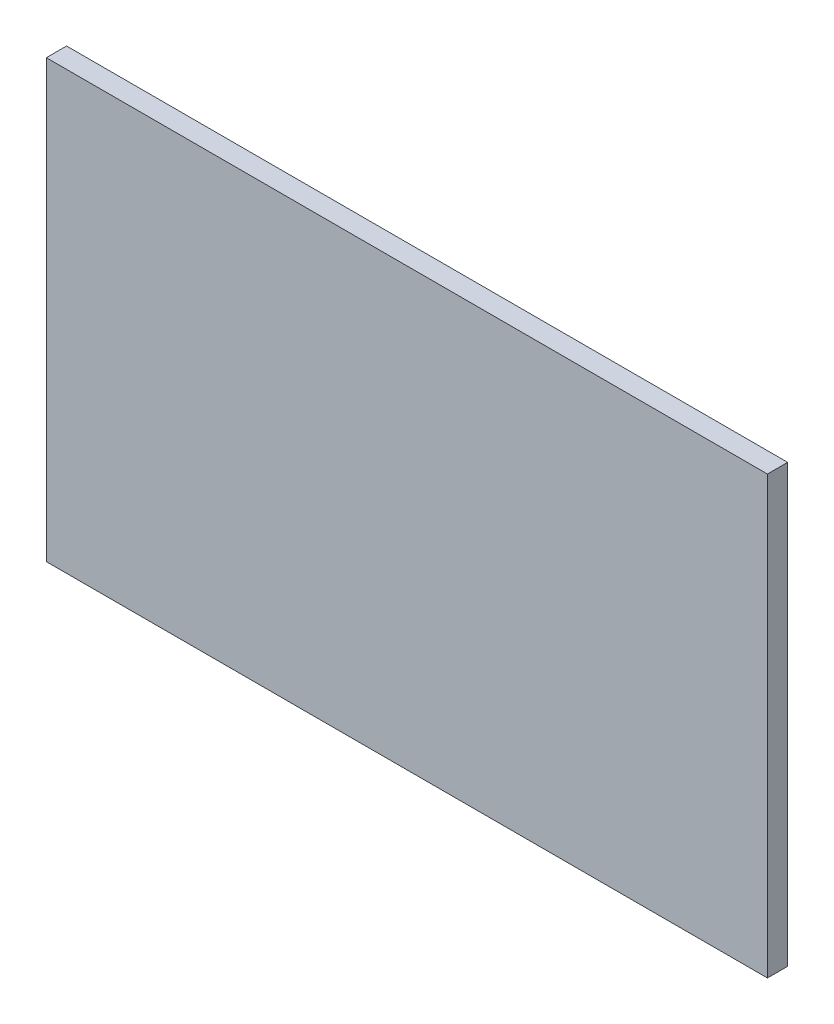
SolidWorks part; units mm, degrees
ref_plane "Front Plane" through (0, 0, 0) normal (0, 0, 1) x (1, 0, 0)
ref_plane "Top Plane" through (0, 0, 0) normal (0, 1, 0) x (1, 0, 0)
ref_plane "Right Plane" through (0, 0, 0) normal (1, 0, 0) x (0, 0, -1)
sketch "Sketch1" plane through (0, 0, 0) normal (0, 0, 1) x (1, 0, 0)
  line L1 (-39.9949, 55.4949) -> (17.0051, 55.4949)
  line L2 (-39.9949, 55.4949) -> (-39.9949, 20.9949)
  line L3 (-39.9949, 20.9949) -> (17.0051, 20.9949)
  line L4 (17.0051, 55.4949) -> (17.0051, 20.9949)
  dimension "D1" = 57
  dimension "D2" = 34.5
extrude "Boss-Extrude1" add sketch "Sketch1" along normal blind 1.6
